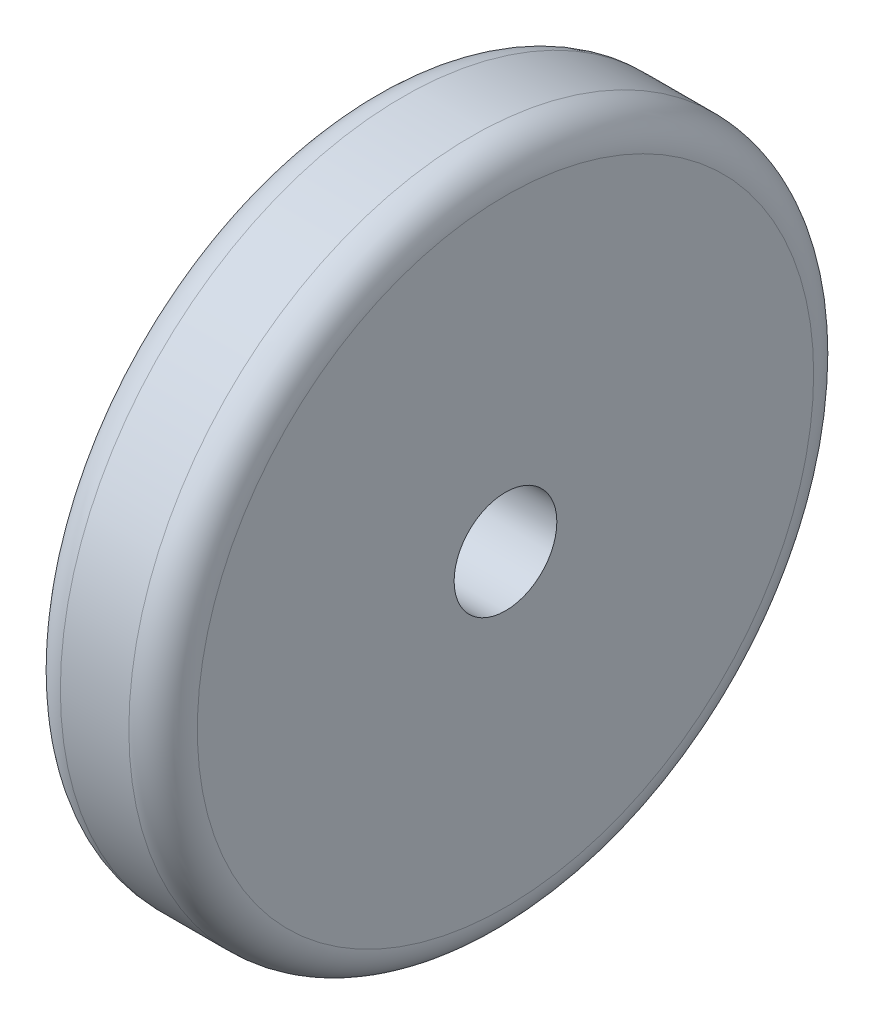
SolidWorks part; units mm, degrees
material "6061 合金"
ref_plane "前视基准面" through (0, 0, 0) normal (0, 0, 1) x (1, 0, 0)
ref_plane "上视基准面" through (0, 0, 0) normal (0, 1, 0) x (1, 0, 0)
ref_plane "右视基准面" through (0, 0, 0) normal (1, 0, 0) x (0, 0, -1)
sketch "草图1" plane through (0, 0, 0) normal (1, 0, 0) x (0, 0, -1)
  circle A0 centre (0, 0) radius 50
  dimension "D1" = 100
extrude "凸台-拉伸1" add sketch "草图1" along normal blind 20
fillet "圆角1" radius 5 2 edges at (0, 0, -50) (20, 0, -50)
sketch "草图2" plane through (0, 0, 0) normal (-1, 0, 0) x (0, 0, 1)
  circle A0 centre (0, 0) radius 7.5
  dimension "D1" = 15
extrude "切除-拉伸1" cut sketch "草图2" against normal blind 30
